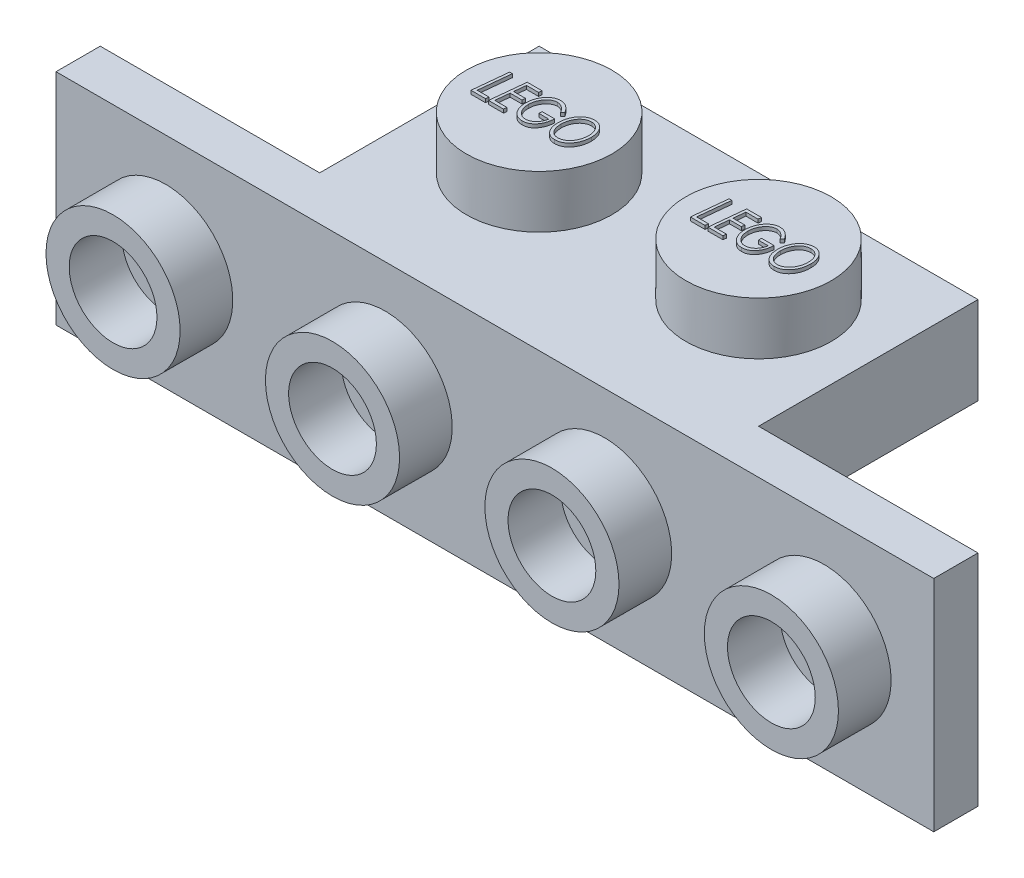
SolidWorks part; units mm, degrees
ref_plane "Front Plane" through (0, 0, 0) normal (0, 0, 1) x (1, 0, 0)
ref_plane "Top Plane" through (0, 0, 0) normal (0, 1, 0) x (1, 0, 0)
ref_plane "Right Plane" through (0, 0, 0) normal (1, 0, 0) x (0, 0, -1)
sketch "Sketch2" plane through (0, 0, 0) normal (0, 1, 0) x (1, 0, 0)
  line L0 (-17.7331, 8.7234) -> (-1.8581, 8.7234)
  line L1 (-1.8581, 8.7234) -> (-1.8581, 0.7859)
  line L2 (-1.8581, 0.7859) -> (-17.7331, 0.7859)
  line L3 (-17.7331, 0.7859) -> (-17.7331, 8.7234)
  dimension "D1" = 15.875
  dimension "D2" = 7.9375
extrude "Boss-Extrude3" add sketch "Sketch2" along normal blind 3.175
sketch "Sketch3" plane through (0, 3.175, 0) normal (0, 1, 0) x (1, 0, 0)
  line L0 (-17.7331, 8.7234) -> (-17.7331, 0.7859) construction
  line L1 (-1.8581, 8.7234) -> (-17.7331, 8.7234) construction
  circle A0 centre (-13.7644, 4.7546) radius 2.6308
  dimension "D1" = 3.9687
  dimension "D2" = 3.9688
extrude "Boss-Extrude4" add sketch "Sketch3" along normal blind 1.905
pattern_linear "LPattern1" count 2 spacing 7.9375 along (1, 0, 0) of "Boss-Extrude4"
shell "Shell1" thickness 1.524
sketch "Sketch4" plane through (0, 5.08, 0) normal (0, 1, 0) x (1, 0, 0)
  line L1 (-13.7644, 4.7546) -> (-13.7644, 4.0766) construction
  line L2 (-15.584, 4.0766) -> (-11.9447, 4.0766) construction
  text T0 "<i>LEGO</i>" font "Century Gothic" height 1.27
  point P4 (-13.7644, 4.7546)
  point P9 (-13.7644, 4.0766)
extrude "Boss-Extrude5" add sketch "Sketch4" along normal blind 0.127
pattern_linear "LPattern2" count 2 spacing 7.9375 along (1, 0, 0) of "Boss-Extrude5"
sketch "Sketch5" plane through (0, 0, 0) normal (0, -1, 0) x (1, 0, 0)
  circle A0 centre (-9.7956, -4.7546) radius 1.4986
  circle A1 centre (-9.7956, -4.7546) radius 0.635
  dimension "D1" = 2.9972
  dimension "D2" = 1.27
extrude "Boss-Extrude6" add sketch "Sketch5" against normal up to surface (1.651 mm away) up to face at (-5.8269, 1.651, -5.8614)
sketch "Sketch6" plane through (0, 0, -0.7859) normal (0, 0, 1) x (1, 0, 0)
  line L0 (-25.6706, 3.175) -> (6.0794, 3.175)
  line L2 (6.0794, 3.175) -> (6.0794, -4.7625)
  line L3 (6.0794, -4.7625) -> (-25.6706, -4.7625)
  line L4 (-25.6706, -4.7625) -> (-25.6706, 3.175)
  point P3 (-9.7956, 3.175)
  dimension "D1" = 31.75
  dimension "D2" = 7.9375
extrude "Boss-Extrude7" add sketch "Sketch6" along normal blind 1.6002
sketch "Sketch7" plane through (0, 0, 0.8143) normal (0, 0, 1) x (1, 0, 0)
  line L0 (-25.6706, 3.175) -> (-25.6706, -4.7625) construction
  circle A0 centre (-21.7019, -0.7938) radius 2.4257
  circle A1 centre (-21.7019, -0.7938) radius 1.5875
  dimension "D2" = 4.8514
  dimension "D3" = 3.175
  dimension "D1" = 3.9688
extrude "Boss-Extrude8" add sketch "Sketch7" along normal blind 1.905
pattern_linear "LPattern3" count 4 spacing 7.9375 along (1, 0, 0) of "Boss-Extrude8"
